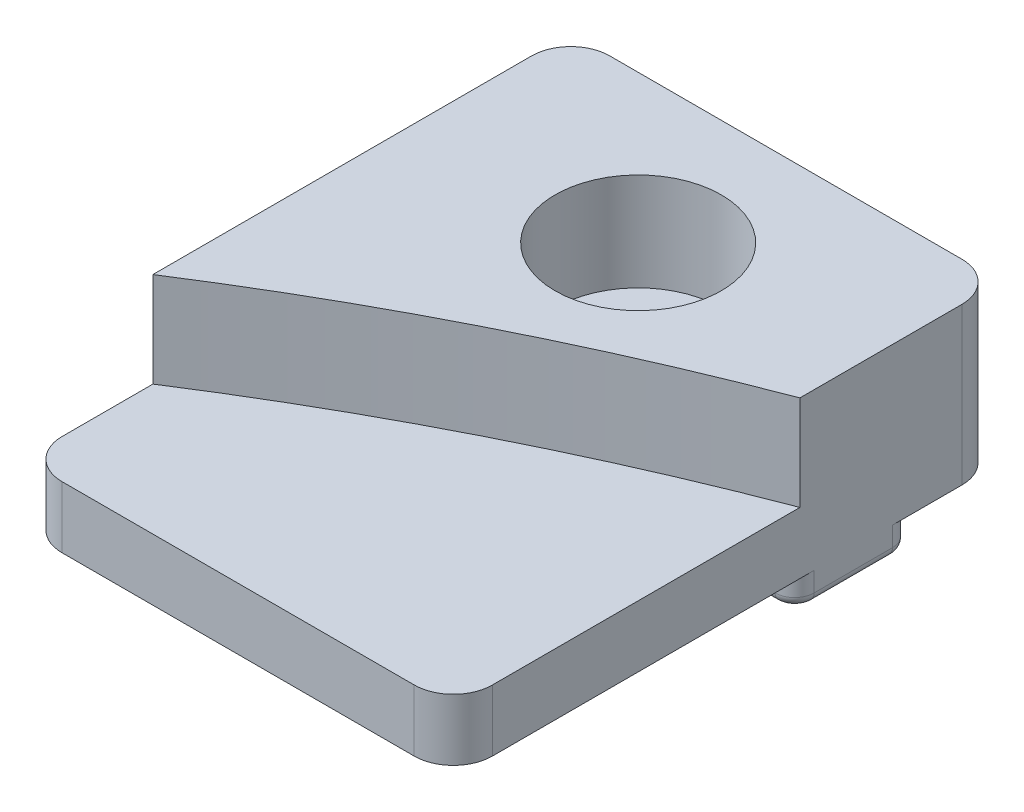
SolidWorks part; units mm, degrees
ref_plane "Front Plane" through (0, 0, 0) normal (0, 0, 1) x (1, 0, 0)
ref_plane "Top Plane" through (0, 0, 0) normal (0, 1, 0) x (1, 0, 0)
ref_plane "Right Plane" through (0, 0, 0) normal (1, 0, 0) x (0, 0, -1)
ref_plane "Plane1" through (0, 8, 0) normal (0, 1, 0) x (1, 0, 0)
sketch "Sketch1" plane through (0, 8, 0) normal (0, 1, 0) x (1, 0, 0)
  line L0 (11, -14) -> (11, 14)
  line L1 (11, 14) -> (-11, 14)
  line L2 (-11, 14) -> (-11, -14)
  line L3 (-11, -14) -> (11, -14)
extrude "Boss-Extrude1" add sketch "Sketch1" against normal blind 9.5
sketch "Sketch2" plane through (11, 0, 0) normal (1, 0, 0) x (0, 0, -1)
  line L0 (3.45, -1.5) -> (3.45, 0)
  line L1 (3.45, 0) -> (-14, 0)
  line L2 (-14, 0) -> (-14, -1.5)
  line L3 (-14, -1.5) -> (3.45, -1.5)
extrude "Cut-Extrude1" cut sketch "Sketch2" against normal through all
sketch "Sketch3" plane through (0, 8, 0) normal (0, 1, 0) x (-1, 0, 0)
  line L0 (11, 7.3586) -> (11, 14)
  line L1 (11, 14) -> (-11, 14)
  line L2 (-11, 14) -> (-11, -3.7188)
  arc A0 (-11, -3.7188) -> (11, 7.3586) centre (-53.23, 107.536) ccw
extrude "Cut-Extrude2" cut sketch "Sketch3" against normal blind 4.85
sketch "Sketch4" plane through (11, 0, 0) normal (1, 0, 0) x (0, 0, -1)
  line L0 (14, -1.5) -> (14, 0)
  line L1 (14, 0) -> (9.45, 0)
  line L2 (9.45, 0) -> (9.45, -1.5)
  line L3 (9.45, -1.5) -> (14, -1.5)
extrude "Cut-Extrude3" cut sketch "Sketch4" against normal through all
hole_wizard "CBORE for M4 Hex Head Machine Screw1" positions "Sketch6" profile "Sketch5" counterbore size "M4" standard "ANSI Metric"
sketch "Sketch6" plane through (0, 8, 0) normal (0, 1, 0) x (1, 0, 0)
  point P0 (0, 6.45)
sketch "Sketch5" plane through (0, 8, -6.45) normal (1, 0, 0) x (0, 0, 1)
  line L0 (0, 0) -> (0, 9.5)
  line L1 (0, 9.5) -> (2.15, 9.5)
  line L3 (2.15, 9.5) -> (2.15, 5)
  line L4 (2.15, 5) -> (4.25, 5)
  line L5 (4.25, 5) -> (4.25, 0)
  line L7 (4.25, 0) -> (0, 0)
  line L11 (0, -6.35) -> (0, 107.95) construction
  dimension "Thru Hole Dia." = 4.3
  dimension "Thru Hole Depth" = 9.5
  dimension "C'Bore Dia." = 8.5
  dimension "C'Bore Depth" = 5
fillet "Fillet1" radius 1 4 edges at (11, -0.75, -3.45) (-11, -0.75, -3.45) (11, -0.75, -9.45) (-11, -0.75, -9.45)
fillet "Fillet2" radius 0.5 8 edges at (10.7071, -1.5, -3.7429) (11, -1.5, -6.45) (0, -1.5, -3.45) (10.7071, -1.5, -9.1571) (-10.7071, -1.5, -3.7429) (0, -1.5, -9.45) (-11, -1.5, -6.45) (-10.7071, -1.5, -9.1571)
fillet "Fillet3" radius 2 4 edges at (-11, 1.575, 14) (11, 1.575, 14) (-11, 4, -14) (11, 4, -14)
